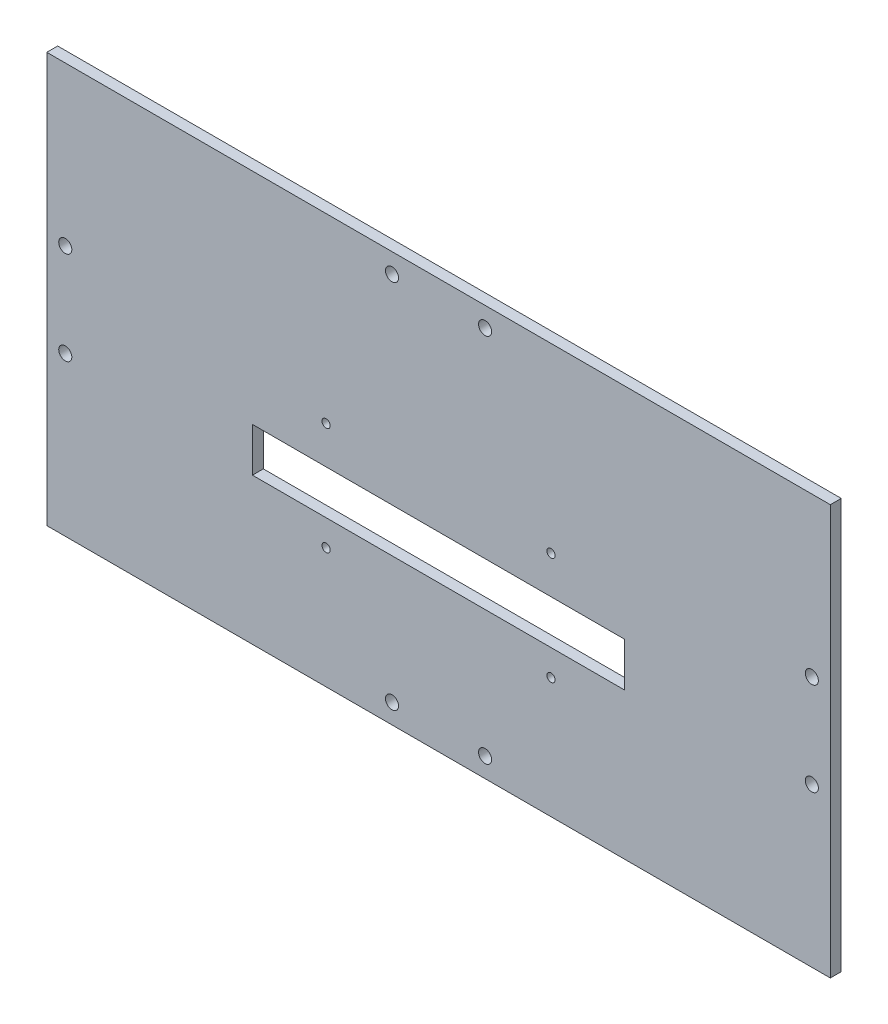
SolidWorks part; units mm, degrees
material "6061-T6 (SS)"
ref_plane "Front Plane" through (0, 0, 0) normal (0, 0, 1) x (1, 0, 0)
ref_plane "Top Plane" through (0, 0, 0) normal (0, 1, 0) x (1, 0, 0)
ref_plane "Right Plane" through (0, 0, 0) normal (1, 0, 0) x (0, 0, -1)
sketch "Sketch1" plane through (0, 0, 0) normal (0, 0, 1) x (1, 0, 0)
  line L0 (-108.712, 13.5509) -> (-108.712, -13.5509) construction
  line L1 (-114.0968, -59.69) -> (114.0968, -59.69)
  line L2 (-114.0968, -59.69) -> (-114.0968, 59.69)
  line L3 (-114.0968, 59.69) -> (114.0968, 59.69)
  line L4 (114.0968, -59.69) -> (114.0968, 59.69)
  line L5 (-114.0968, -59.69) -> (114.0968, 59.69) construction
  line L6 (-114.0968, 59.69) -> (114.0968, -59.69) construction
  line L7 (-108.712, 0) -> (-114.0968, 0) construction
  line L8 (0, 0) -> (0, 59.69) construction
  line L9 (0, -24.588) -> (0, 0) construction
  line L10 (-32.75, -24.588) -> (32.75, -24.588) construction
  line L11 (-32.75, -24.588) -> (-32.75, 6.762) construction
  line L12 (-32.75, 6.762) -> (32.75, 6.762) construction
  line L13 (32.75, -24.588) -> (32.75, 6.762) construction
  line L14 (0, -18.288) -> (0, -24.588) construction
  line L15 (-58, -2.938) -> (58, -2.938) construction
  line L16 (-58, -2.938) -> (-58, -18.288) construction
  line L17 (-58, -18.288) -> (58, -18.288) construction
  line L18 (58, -2.938) -> (58, -18.288) construction
  line L19 (-13.5509, 53.975) -> (13.5509, 53.975) construction
  line L20 (-54.2, -17.018) -> (54.2, -17.018)
  line L21 (-54.2, -17.018) -> (-54.2, -4.208)
  line L22 (-54.2, -4.208) -> (54.2, -4.208)
  line L23 (54.2, -17.018) -> (54.2, -4.208)
  line L24 (-54.2, -17.018) -> (54.2, -4.208) construction
  line L25 (-54.2, -4.208) -> (54.2, -17.018) construction
  line L26 (0, 0) -> (-108.712, 0) construction
  circle A0 centre (-108.712, 13.5509) radius 1.905
  circle A1 centre (-108.712, -13.5509) radius 1.905
  circle A2 centre (108.712, -13.5509) radius 1.905
  circle A3 centre (108.712, 13.5509) radius 1.905
  circle A4 centre (-32.75, 6.762) radius 1.2
  circle A5 centre (32.75, 6.762) radius 1.2
  circle A6 centre (32.75, -24.588) radius 1.2
  circle A7 centre (-32.75, -24.588) radius 1.2
  circle A8 centre (-13.5509, 53.975) radius 1.905
  circle A9 centre (13.5509, 53.975) radius 1.905
  circle A10 centre (13.5509, -53.975) radius 1.905
  circle A11 centre (-13.5509, -53.975) radius 1.905
  point P31 (0, -10.613)
  dimension "D3" = 108.712
  dimension "D6" = 31.35
  dimension "D9" = 41.402
  dimension "D4" = 3.81
  dimension "D8" = 2.4
  dimension "D1" = 228.1936
  dimension "D2" = 119.38
  dimension "D5" = 27.1018
  dimension "D7" = 65.5
  dimension "D10" = 6.3
  dimension "D11" = 15.35
  dimension "D12" = 116
  dimension "D13" = 108.4
  dimension "D14" = 1.27
  dimension "D15" = 1.27
  dimension "D16" = 13.5509
  dimension "D17" = 5.715
extrude "Boss-Extrude1" add sketch "Sketch1" along normal blind 3.175
